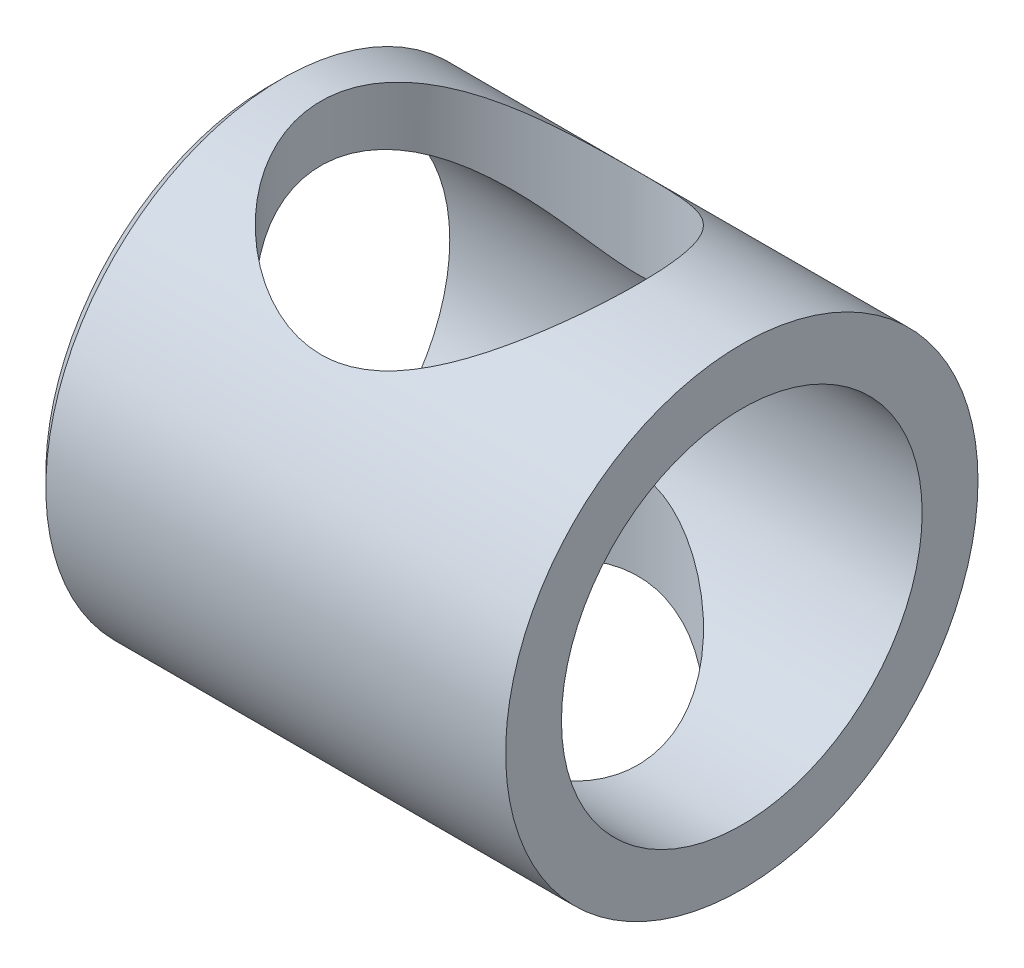
SolidWorks part; units mm, degrees
ref_plane "Front Plane" through (0, 0, 0) normal (0, 0, 1) x (1, 0, 0)
ref_plane "Top Plane" through (0, 0, 0) normal (0, 1, 0) x (1, 0, 0)
ref_plane "Right Plane" through (0, 0, 0) normal (1, 0, 0) x (0, 0, -1)
sketch "Sketch1" plane through (0, 0, 0) normal (1, 0, 0) x (0, 0, -1)
  circle A0 centre (0, 0) radius 10.9093
  circle A1 centre (0, 0) radius 14.2875
  dimension "D1" = 21.8186
  dimension "D2" = 28.575
extrude "Boss-Extrude1" add sketch "Sketch1" along normal blind 28.575
sketch "Sketch2" plane through (0, 0, 0) normal (0, 1, 0) x (1, 0, 0)
  line L0 (0, 0) -> (12.7, 0) construction
  circle A0 centre (12.7, 0) radius 9.5885
  dimension "D1" = 19.177
  dimension "D2" = 12.7
extrude "Cut-Extrude1" cut sketch "Sketch2" against normal mid plane 38.1
chamfer "Chamfer1" distance 0.762 angle 45 1 edges at (0, 0, -14.2875)
